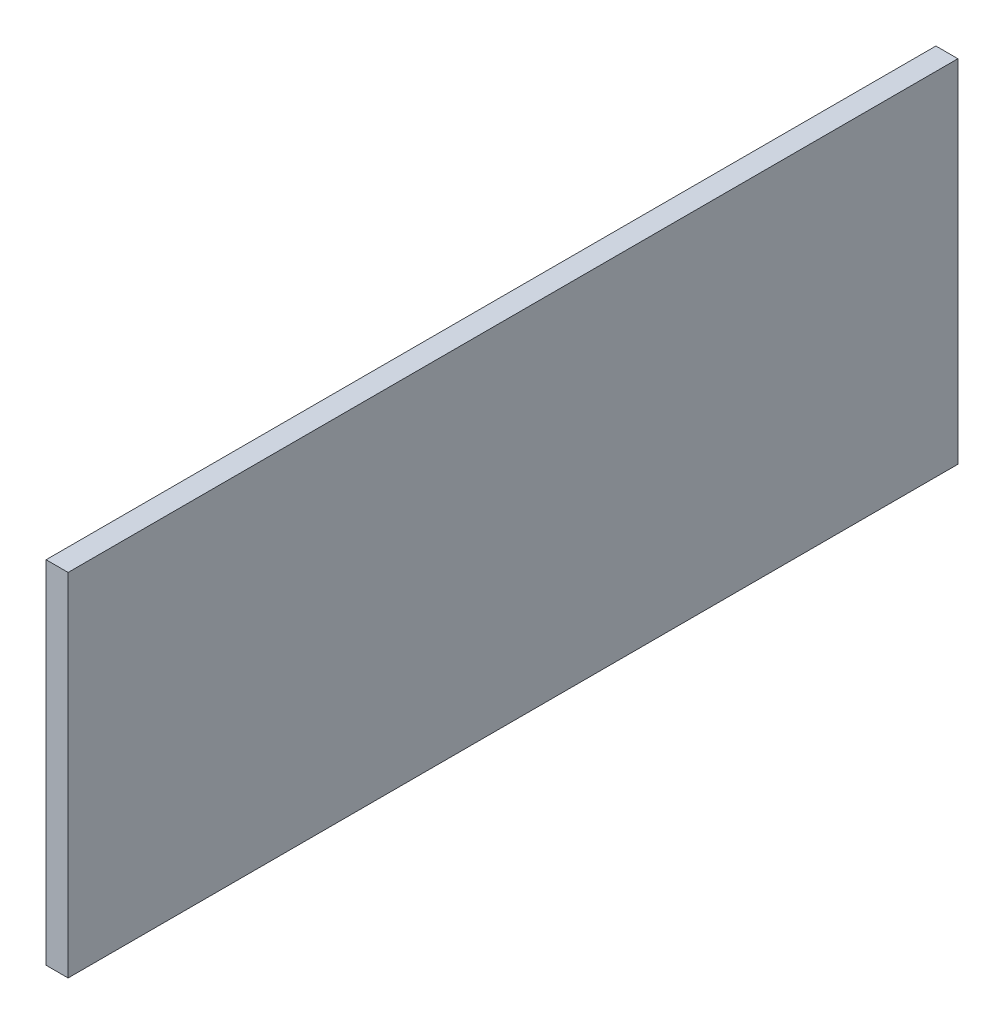
SolidWorks part; units mm, degrees
ref_plane "Front Plane" through (0, 0, 0) normal (0, 0, 1) x (1, 0, 0)
ref_plane "Top Plane" through (0, 0, 0) normal (0, 1, 0) x (1, 0, 0)
ref_plane "Right Plane" through (0, 0, 0) normal (1, 0, 0) x (0, 0, -1)
sketch "Sketch1" plane through (0, 0, 0) normal (1, 0, 0) x (0, 0, -1)
  line L1 (-241.3, -95.25) -> (241.3, -95.25)
  line L2 (-241.3, -95.25) -> (-241.3, 95.25)
  line L3 (-241.3, 95.25) -> (241.3, 95.25)
  line L4 (241.3, -95.25) -> (241.3, 95.25)
  line L5 (-241.3, -95.25) -> (241.3, 95.25) construction
  line L6 (-241.3, 95.25) -> (241.3, -95.25) construction
  point P0 (0, 0)
  dimension "D1" = 190.5
  dimension "D2" = 482.6
extrude "Boss-Extrude1" add sketch "Sketch1" along normal blind 11.938
